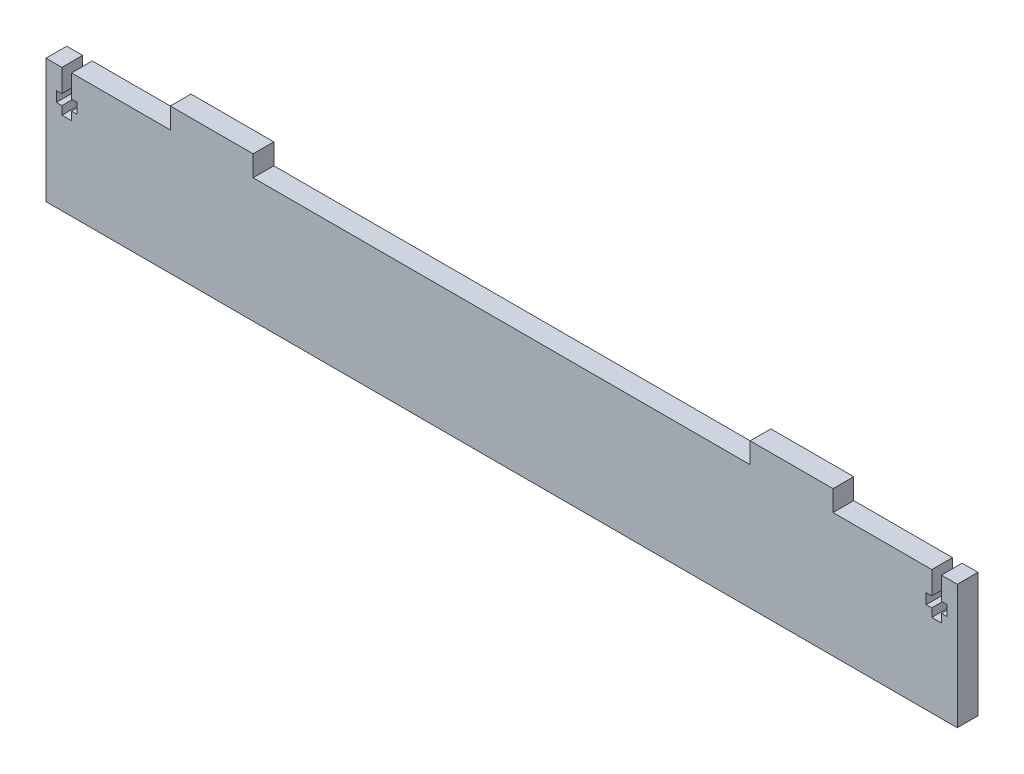
SolidWorks part; units mm, degrees
ref_plane "Front Plane" through (0, 0, 0) normal (0, 0, 1) x (1, 0, 0)
ref_plane "Top Plane" through (0, 0, 0) normal (0, 1, 0) x (1, 0, 0)
ref_plane "Right Plane" through (0, 0, 0) normal (1, 0, 0) x (0, 0, -1)
sketch "Sketch1" plane through (0, 0, 0) normal (0, 0, 1) x (1, 0, 0)
  line L0 (-101.6, 19.05) -> (-101.6, 25.4)
  line L1 (-139.7, 19.05) -> (-101.6, 19.05)
  line L2 (-139.7, 19.05) -> (-139.7, -19.05)
  line L3 (-139.7, -19.05) -> (139.7, -19.05)
  line L4 (139.7, 19.05) -> (139.7, -19.05)
  line L5 (-139.7, 19.05) -> (139.7, -19.05) construction
  line L6 (-139.7, -19.05) -> (139.7, 19.05) construction
  line L7 (-101.6, 25.4) -> (-76.2, 25.4)
  line L8 (-76.2, 25.4) -> (-76.2, 19.05)
  line L9 (-76.2, 19.05) -> (76.2, 19.05)
  line L10 (0, 60.3217) -> (0, -57.4102) construction
  line L11 (76.2, 25.4) -> (76.2, 19.05)
  line L12 (101.6, 25.4) -> (76.2, 25.4)
  line L13 (101.6, 19.05) -> (101.6, 25.4)
  line L14 (101.6, 19.05) -> (139.7, 19.05)
  point P0 (0, 0)
  dimension "D1" = 279.4
  dimension "D2" = 38.1
  dimension "D3" = 25.4
  dimension "D4" = 6.35
  dimension "D5" = 76.2
extrude "Boss-Extrude1" add sketch "Sketch1" along normal blind 6.35
sketch "Sketch2" plane through (0, 0, 6.35) normal (0, 0, 1) x (1, 0, 0)
  line L0 (-134.8232, 19.05) -> (-134.8232, 12.065)
  line L1 (-101.6, 19.05) -> (-139.7, 19.05) construction
  line L2 (-134.8232, 12.065) -> (-136.525, 12.065)
  line L3 (-136.525, 12.065) -> (-136.525, 8.89)
  line L4 (-136.525, 8.89) -> (-134.8232, 8.89)
  line L5 (-134.8232, 8.89) -> (-134.8232, 6.35)
  line L6 (-134.8232, 6.35) -> (-131.8768, 6.35)
  line L7 (-131.8768, 6.35) -> (-131.8768, 8.89)
  line L8 (-131.8768, 8.89) -> (-130.175, 8.89)
  line L9 (-130.175, 8.89) -> (-130.175, 12.065)
  line L10 (-130.175, 12.065) -> (-131.8768, 12.065)
  line L11 (-131.8768, 12.065) -> (-131.8768, 19.05)
  line L12 (-133.35, 6.35) -> (-133.35, 23.6811) construction
  line L13 (-139.7, 19.05) -> (-139.7, -19.05) construction
  line L14 (0, 37.1191) -> (0, -25.8621) construction
  line L15 (133.35, 6.35) -> (133.35, 23.6811) construction
  line L16 (131.8768, 12.065) -> (131.8768, 19.05)
  line L17 (130.175, 12.065) -> (131.8768, 12.065)
  line L18 (130.175, 8.89) -> (130.175, 12.065)
  line L19 (131.8768, 8.89) -> (130.175, 8.89)
  line L20 (131.8768, 6.35) -> (131.8768, 8.89)
  line L21 (134.8232, 6.35) -> (131.8768, 6.35)
  line L22 (134.8232, 8.89) -> (134.8232, 6.35)
  line L23 (136.525, 8.89) -> (134.8232, 8.89)
  line L24 (136.525, 12.065) -> (136.525, 8.89)
  line L25 (134.8232, 12.065) -> (136.525, 12.065)
  line L26 (134.8232, 19.05) -> (134.8232, 12.065)
  line L27 (-134.8232, 19.05) -> (-131.8768, 19.05)
  line L28 (131.8768, 19.05) -> (134.8232, 19.05)
  dimension "D1" = 3.175
  dimension "D2" = 12.7
  dimension "D3" = 2.54
  dimension "D4" = 6.35
  dimension "D5" = 2.9464
  dimension "D6" = 6.35
extrude "Cut-Extrude1" cut sketch "Sketch2" against normal blind 6.35
